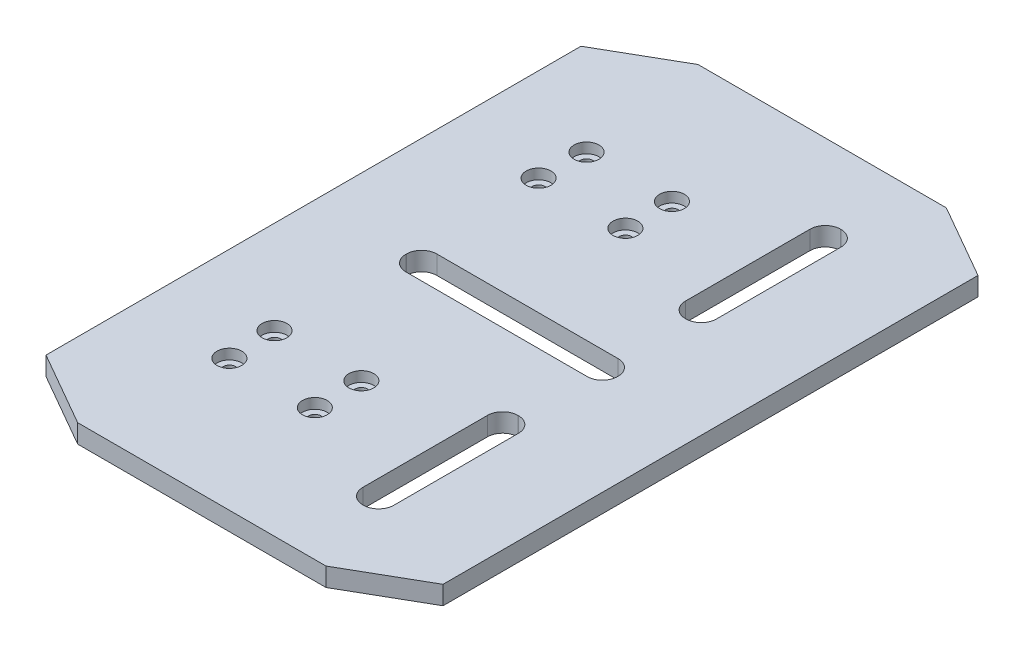
SolidWorks part; units mm, degrees
material "Custom Plastic"
ref_plane "Front Plane" through (0, 0, 0) normal (0, 0, 1) x (1, 0, 0)
ref_plane "Top Plane" through (0, 0, 0) normal (0, 1, 0) x (1, 0, 0)
ref_plane "Right Plane" through (0, 0, 0) normal (1, 0, 0) x (0, 0, -1)
sketch "Sketch1" plane through (0, 0, 0) normal (0, 1, 0) x (1, 0, 0)
  line L0 (-32, -43.1177) -> (-20.0119, -50)
  line L1 (-20.0119, -50) -> (20.0119, -50)
  line L2 (-32, -43.1177) -> (-32, 43.1177)
  line L3 (-20.0119, 50) -> (20.0119, 50)
  line L4 (32, -43.1177) -> (32, 43.1177)
  line L5 (-28.8545, -44.9235) -> (28.8545, 44.9235) construction
  line L6 (-28.4421, 45.1603) -> (28.4421, -45.1603) construction
  line L7 (-114.8204, 0) -> (150.9847, 0) construction
  line L8 (0, -72.5189) -> (0, 84.1411) construction
  line L9 (32, -43.1177) -> (20.0119, -50)
  line L10 (32, 43.1177) -> (20.0119, 50)
  line L11 (-32, 43.1177) -> (-20.0119, 50)
  point P0 (0, 0)
  dimension "D1" = 64
  dimension "D2" = 100
extrude "Boss-Extrude1" add sketch "Sketch1" along normal blind 3
sketch "Sketch5" plane through (0, 3, 0) normal (0, 1, 0) x (1, 0, 0)
  line L0 (-100.8141, 0) -> (111.641, 0) construction
  line L1 (14.5, 50) -> (14.5, -50) construction
  line L2 (-14.6202, -2.5) -> (14.6202, -2.5)
  line L3 (-17.0702, -0.05) -> (-17.0702, 0.05)
  line L4 (-14.6202, 2.5) -> (14.6202, 2.5)
  line L5 (17.0702, -0.05) -> (17.0702, 0.05)
  line L6 (-17.0702, -2.5) -> (17.0702, 2.5) construction
  line L7 (-17.0702, 2.5) -> (17.0702, -2.5) construction
  line L8 (20.0119, 50) -> (-20.0119, 50) construction
  line L9 (-20.0119, -50) -> (20.0119, -50) construction
  line L10 (14.5, 50) -> (14.5, 0) construction
  line L11 (14.5, 0) -> (14.5, -50) construction
  line L12 (14.45, -38.5) -> (14.55, -38.5)
  line L13 (14.45, 13.5) -> (14.55, 13.5)
  line L14 (12, 15.95) -> (12, 36.05)
  line L15 (14.45, 38.5) -> (14.55, 38.5)
  line L16 (17, 15.95) -> (17, 36.05)
  line L17 (12, 13.5) -> (17, 38.5) construction
  line L18 (12, 38.5) -> (17, 13.5) construction
  line L19 (12, -15.95) -> (12, -36.05)
  line L20 (14.45, -13.5) -> (14.55, -13.5)
  line L21 (17, -15.95) -> (17, -36.05)
  line L22 (32, -43.1177) -> (32, 43.1177) construction
  arc A0 (14.45, -38.5) -> (12, -36.05) centre (14.45, -36.05) cw
  arc A1 (14.55, -38.5) -> (17, -36.05) centre (14.55, -36.05) ccw
  arc A2 (12, -15.95) -> (14.45, -13.5) centre (14.45, -15.95) cw
  arc A3 (14.55, -13.5) -> (17, -15.95) centre (14.55, -15.95) cw
  arc A4 (-14.6202, -2.5) -> (-17.0702, -0.05) centre (-14.6202, -0.05) cw
  arc A5 (-17.0702, 0.05) -> (-14.6202, 2.5) centre (-14.6202, 0.05) cw
  arc A6 (14.6202, 2.5) -> (17.0702, 0.05) centre (14.6202, 0.05) cw
  arc A7 (14.6202, -2.5) -> (17.0702, -0.05) centre (14.6202, -0.05) ccw
  arc A8 (14.55, 13.5) -> (17, 15.95) centre (14.55, 15.95) ccw
  arc A9 (14.45, 13.5) -> (12, 15.95) centre (14.45, 15.95) cw
  arc A10 (12, 36.05) -> (14.45, 38.5) centre (14.45, 36.05) cw
  arc A11 (14.55, 38.5) -> (17, 36.05) centre (14.55, 36.05) cw
  point P3 (0, 0)
  point P14 (14.5, 0)
  point P15 (14.5, 26)
  point P17 (14.5, -26)
  point P18 (14.5, 26)
  point P31 (12, -38.5)
  point P34 (17, -38.5)
  point P37 (12, -13.5)
  point P40 (17, -13.5)
  dimension "D7" = 2.45
  dimension "D1" = 5
  dimension "D2" = 26
  dimension "D3" = 26
  dimension "D4" = 5
  dimension "D5" = 25
  dimension "D6" = 15
extrude "Cut-Extrude2" cut sketch "Sketch5" against normal blind 10
sketch "Sketch7" plane through (0, 3, 0) normal (0, 1, 0) x (1, 0, 0)
  line L4 (-24, 17.035) -> (-24, 35.535)
  line L5 (4, 17.035) -> (-24, 17.035)
  line L6 (4, 35.535) -> (-24, 35.535)
  line L7 (4, 17.035) -> (4, 35.535)
  line L9 (-23.2876, 32.535) -> (3.7524, 32.535)
  line L10 (-23.7676, 25.035) -> (4.2324, 25.035)
  line L11 (-10, 43.5449) -> (-10, 10.5144) construction
  line L12 (-17, 43.5449) -> (-17, 10.5144) construction
  line L13 (-16.7676, 32.535) -> (-16.7676, 25.035) construction
  line L14 (-23.7676, 28.785) -> (4.2324, 28.785) construction
  line L16 (-32, 43.1177) -> (-32, -43.1177) construction
  circle A0 centre (-16.7676, 28.785) radius 1
  circle A1 centre (-3, 28.785) radius 1
  circle A2 centre (-17, 21.285) radius 1
  circle A3 centre (-3, 21.285) radius 1
  point P12 (-16.7676, 25.035)
  point P17 (-17, 28.785)
  dimension "D5" = 2
  dimension "D1" = 7.5
  dimension "D2" = 7
  dimension "D3" = 14
  dimension "D4" = 3.75
  dimension "D6" = 28
  dimension "D7" = 8
  dimension "D8" = 14
  dimension "D9" = 14
  dimension "D10" = 7.5
  dimension "D11" = 7.5
  dimension "D12" = 7
ref_plane "Plane1" through (0, 0, 0) normal (0, 0, -1) x (-1, 0, 0)
extrude "Cut-Extrude3" cut sketch "Sketch7" against normal blind 11.5 contours A1 | A3 | A2 | A0
ref_plane "Plane2" through (0, 0, 0) normal (0, 0, -1) x (-1, 0, 0)
mirror "Mirror1" about plane through (0, 0, 0) normal (0, 0, -1) of "Cut-Extrude3"
sketch "Sketch8" plane through (0, 3, 0) normal (0, 1, 0) x (1, 0, 0)
  circle A0 centre (-3, -28.785) radius 2
  circle A1 centre (-16.7676, -28.785) radius 2
  circle A2 centre (-17, -21.285) radius 2
  circle A3 centre (-3, -21.285) radius 2
  circle A4 centre (-3, 28.785) radius 2
  circle A5 centre (-3, 21.285) radius 2
  circle A6 centre (-17, 21.285) radius 2
  circle A7 centre (-16.7676, 28.785) radius 2
  dimension "D1" = 4
  dimension "D2" = 4
  dimension "D3" = 4
  dimension "D4" = 4
  dimension "D5" = 4
  dimension "D6" = 4
  dimension "D7" = 4
  dimension "D8" = 4
extrude "Cut-Extrude4" cut sketch "Sketch8" against normal blind 1.65
